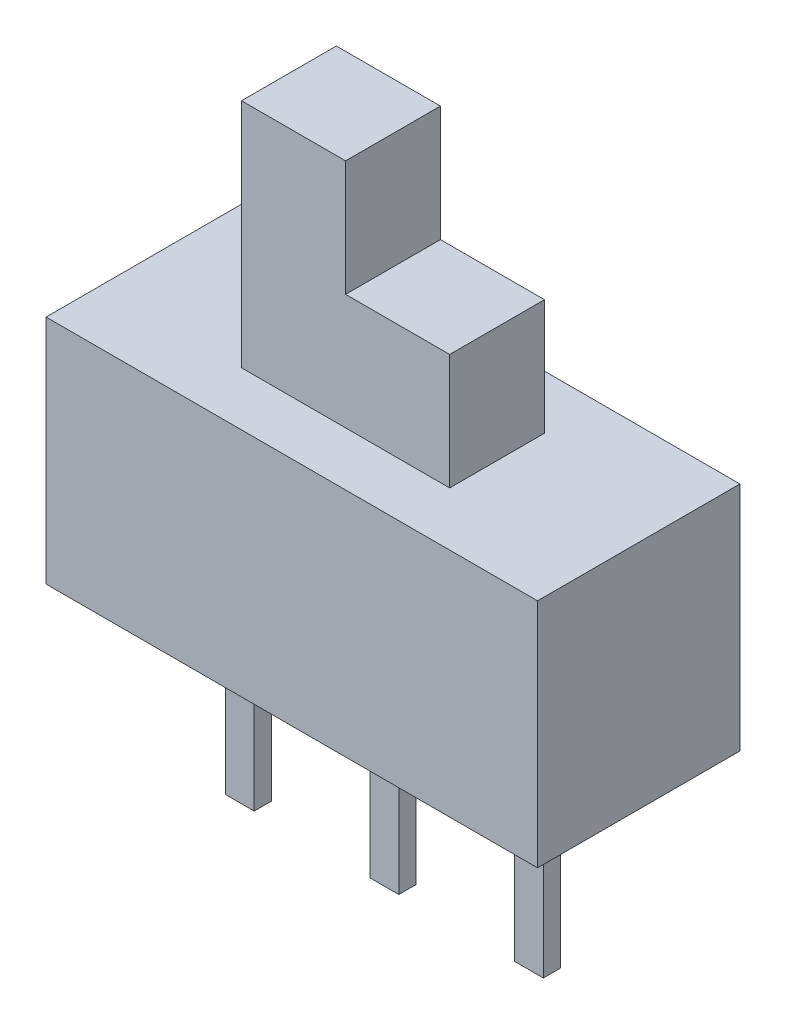
SolidWorks part; units mm, degrees
ref_plane "前视基准面" through (0, 0, 0) normal (0, 0, 1) x (1, 0, 0)
ref_plane "上视基准面" through (0, 0, 0) normal (0, 1, 0) x (1, 0, 0)
ref_plane "右视基准面" through (0, 0, 0) normal (1, 0, 0) x (0, 0, -1)
sketch "草图1" plane through (0, 0, 0) normal (0, 1, 0) x (1, 0, 0)
  line L1 (-4.25, 1.75) -> (4.25, 1.75)
  line L2 (-4.25, 1.75) -> (-4.25, -1.75)
  line L3 (-4.25, -1.75) -> (4.25, -1.75)
  line L4 (4.25, 1.75) -> (4.25, -1.75)
  line L5 (-4.25, 1.75) -> (4.25, -1.75) construction
  line L6 (-4.25, -1.75) -> (4.25, 1.75) construction
  point P0 (0, 0)
  dimension "D1" = 8.5
  dimension "D2" = 3.5
extrude "凸台-拉伸1" add sketch "草图1" along normal blind 4
sketch "草图2" plane through (0, 4, 0) normal (0, 1, 0) x (1, 0, 0)
  line L0 (0, 0.82) -> (0, 0) construction
  line L1 (-1.8, 0.82) -> (1.8, 0.82)
  line L2 (-1.8, 0.82) -> (-1.8, -0.82)
  line L3 (-1.8, -0.82) -> (1.8, -0.82)
  line L4 (1.8, 0.82) -> (1.8, -0.82)
  line L5 (0, 0) -> (1.8, 0) construction
  dimension "D1" = 3.6
  dimension "D2" = 1.64
extrude "凸台-拉伸2" add sketch "草图2" along normal blind 4
sketch "草图3" plane through (0, 8, 0) normal (0, 1, 0) x (1, 0, 0)
  line L0 (1.8, 0.82) -> (-1.8, 0.82) construction
  line L1 (0, 0.82) -> (1.8, 0.82)
  line L2 (0, 0.82) -> (0, -0.82)
  line L3 (0, -0.82) -> (1.8, -0.82)
  line L4 (1.8, 0.82) -> (1.8, -0.82)
extrude "切除-拉伸1" cut sketch "草图3" against normal blind 2
sketch "草图4" plane through (0, 0, 0) normal (0, -1, 0) x (1, 0, 0)
  line L9 (2.25, 0.15) -> (2.75, 0.15)
  line L21 (-0.25, 0.15) -> (0.25, 0.15)
  line L26 (-0.25, 0.15) -> (-0.25, -0.15)
  line L27 (2.25, 0.15) -> (2.25, -0.15)
  line L28 (2.25, -0.15) -> (2.75, -0.15)
  line L29 (2.75, 0.15) -> (2.75, -0.15)
  line L30 (2.25, 0.15) -> (2.75, -0.15) construction
  line L31 (2.25, -0.15) -> (2.75, 0.15) construction
  line L36 (-0.25, -0.15) -> (0.25, -0.15)
  line L37 (0.25, 0.15) -> (0.25, -0.15)
  line L38 (-2.75, 0.15) -> (-2.25, 0.15)
  line L39 (-2.75, 0.15) -> (-2.75, -0.15)
  line L40 (-2.75, -0.15) -> (-2.25, -0.15)
  line L41 (-2.25, 0.15) -> (-2.25, -0.15)
  line L42 (-2.75, 0.15) -> (-2.25, -0.15) construction
  line L43 (-2.75, -0.15) -> (-2.25, 0.15) construction
  line L44 (-0.25, 0.15) -> (0.25, -0.15) construction
  line L45 (-0.25, -0.15) -> (0.25, 0.15) construction
  point P4 (0, 0)
extrude "凸台-拉伸3" add sketch "草图4" along normal blind 7.2 from surface at -4 starting at face at (0, 4, 0)
